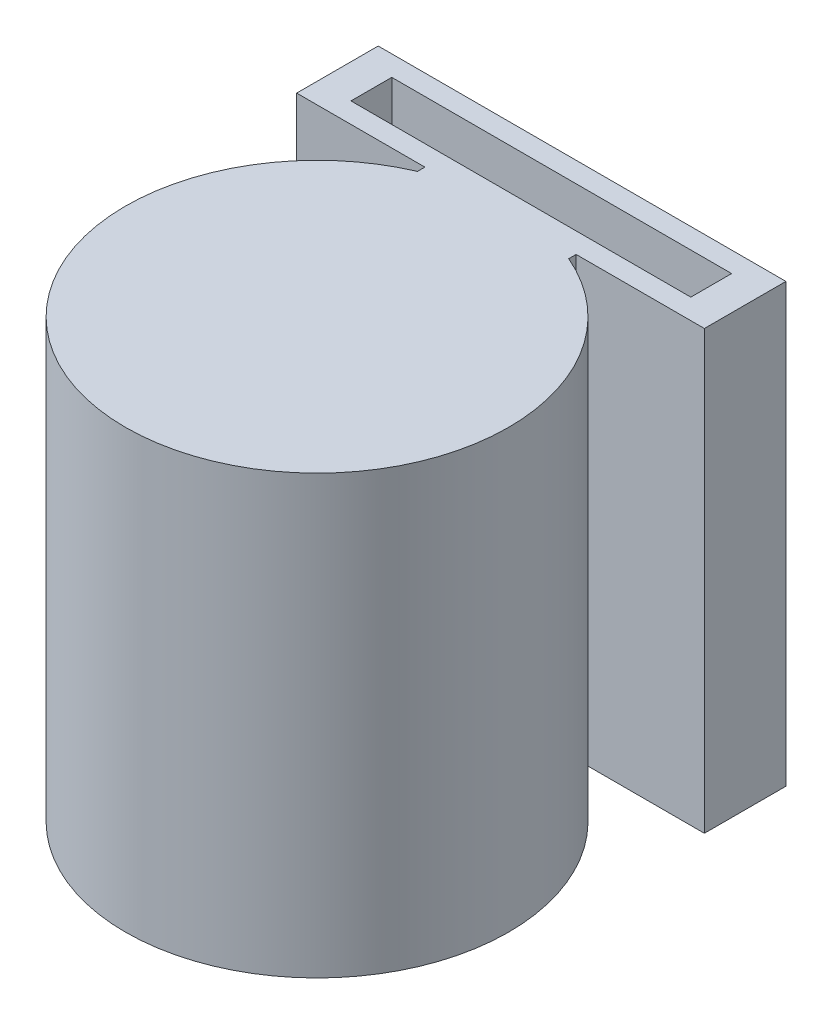
SolidWorks part; units mm, degrees
ref_plane "Alzado" through (0, 0, 0) normal (0, 0, 1) x (1, 0, 0)
ref_plane "Planta" through (0, 0, 0) normal (0, 1, 0) x (1, 0, 0)
ref_plane "Vista lateral" through (0, 0, 0) normal (1, 0, 0) x (0, 0, -1)
sketch "Croquis1" plane through (0, 0, 0) normal (0, 1, 0) x (1, 0, 0)
  line L0 (-15, 28) -> (-15, 22)
  line L1 (-15, 22) -> (15, 22)
  line L2 (15, 22) -> (15, 28)
  line L3 (15, 28) -> (-15, 28)
  line L4 (-12.503, 26.502) -> (-12.503, 23.498)
  line L5 (-12.503, 23.498) -> (12.503, 23.498)
  line L6 (12.503, 23.498) -> (12.503, 26.502)
  line L7 (12.503, 26.502) -> (-12.503, 26.502)
  line L8 (0, 22) -> (0, 0) construction
  dimension "D1" = 30
  dimension "D2" = 6
  dimension "D3" = 2.497
  dimension "D4" = 1.498
  dimension "D5" = 25.006
  dimension "D6" = 3.004
  dimension "D7" = 22
extrude "Saliente-Extruir1" add sketch "Croquis1" against normal blind 32.17 separate body
sketch "Croquis27" plane through (0, 0, -28) normal (0, 0, -1) x (-1, 0, 0)
  line L0 (0, -1.9214) -> (0, -33.4148) construction
  line L2 (14.9659, -17.6681) -> (-14.9659, -17.6681) construction
sketch "Croquis2" plane through (0, 0, -28) normal (0, 0, -1) x (1, 0, 0)
  line L0 (0, 17.6681) -> (4.7642, 17.6681) construction
  line L1 (-12.5, 5.1662) -> (12.5, 5.1662)
  line L2 (-12.5, 5.1662) -> (-12.5, 30.17)
  line L3 (-12.5, 30.17) -> (12.5, 30.17)
  line L4 (12.5, 5.1662) -> (12.5, 30.17)
  line L5 (15, 32.17) -> (15, 0) construction
  line L7 (-14.9659, 17.6681) -> (14.9659, 17.6681) construction
  line L9 (-12.5, 30.17) -> (12.5, 5.1662) construction
  line L10 (12.5, 30.17) -> (-12.5, 5.1662) construction
  line L11 (15, 32.17) -> (-15, 32.17) construction
  dimension "D1" = 2
  dimension "D3" = 2.5
  dimension "D4" = 25
extrude "Cortar-Extruir1" cut sketch "Croquis2" against normal up to surface (1.498 mm away) up to face at (0, -16.085, -26.502)
sketch "Croquis3" plane through (0, 0, 0) normal (0, 1, 0) x (1, 0, 0)
  line L0 (0, 8.4997) -> (0, 22) construction
  line L1 (-15, 22) -> (15, 22) construction
  circle A0 centre (0, 8.4997) radius 14.0984
  circle A1 centre (0, 8.4997) radius 13.1
  dimension "D1" = 26.2
  dimension "D2" = 0.9984
  dimension "D3" = 13.5003
extrude "Saliente-Extruir2" add sketch "Croquis3" against normal up to surface (32.17 mm away) up to face at (0, -32.17, -25)
ref_plane "Plano1" through (0, 0, 5.5987) normal (0, 0, 1) x (1, 0, 0)
sketch "Croquis24" plane through (0, 0, 0) normal (0, 1, 0) x (1, 0, 0)
  line L0 (0, 22) -> (0, 8.4997) construction
  line L1 (-4.0629, 22) -> (4.0629, 22) construction
sketch "Croquis17" plane through (0, 0, 0) normal (1, 0, 0) x (0, 0, -1)
  line L0 (-10.17, -32.17) -> (25.83, 3.83)
  line L2 (25.83, 3.83) -> (25.83, -32.17)
  line L3 (25.83, -32.17) -> (-10.17, -32.17)
  line L4 (22, -32.17) -> (28, -32.17) construction
  dimension "D1" = 36
  dimension "D3" = 45
ref_plane "Plano3" through (0, 0, -25.83) normal (0, 0, -1) x (-1, 0, 0)
sketch "Croquis19" plane through (0, 0, -25.83) normal (0, 0, -1) x (-1, 0, 0)
  line L0 (0, 3.83) -> (21.1813, 3.83)
ref_plane "Plano2" through (0, -11, -11) normal (0, -0.7071, -0.7071) x (-1, 0, 0)
sketch "Croquis10" plane through (0, -11, -11) normal (0, -0.7071, -0.7071) x (-1, 0, 0)
  line L1 (-15.7096, 15.2733) -> (14.4682, 15.2733)
  line L2 (-15.7096, 15.2733) -> (-15.7096, -26.0005)
  line L3 (-15.7096, -26.0005) -> (14.4682, -26.0005)
  line L4 (14.4682, 15.2733) -> (14.4682, -26.0005)
  ellipse E1 centre (0, -16.7374) end of major axis (-13.1, -16.7374) minor radius 9.2631 construction
  ellipse E2 centre (0, 6.0102) end of major axis (13.1, 6.0102) minor radius 9.2631 construction
extrude "Saliente-Extruir4" add sketch "Croquis10" against normal blind 22
sketch "Croquis11" plane through (0, -32.17, 0) normal (0, -1, 0) x (1, 0, 0)
  line L0 (-4.6767, -21.7998) -> (-14.4682, -21.7998)
  line L1 (15.7096, -21.7998) -> (4.6767, -21.7998)
  line L2 (15.7096, -21.7998) -> (15.7096, 22.9415)
  line L3 (15.7096, 22.9415) -> (-14.4682, 22.9415)
  line L4 (-14.4682, -21.7998) -> (-14.4682, 22.9415)
  arc A0 (4.6767, -21.7998) -> (-4.6767, -21.7998) centre (0, -8.4997) ccw
  arc A1 (4.0629, -22) -> (-4.0629, -22) centre (0, -8.4997) ccw construction
extrude "Cortar-Extruir2" cut sketch "Croquis11" against normal blind 58 and the other way blind 10
sketch "Croquis12" plane through (0, 0, 0) normal (1, 0, 0) x (0, 0, -1)
  line L1 (28, 0) -> (-15.0912, 0)
  line L2 (28, 0) -> (28, 18.5635)
  line L3 (28, 18.5635) -> (-15.0912, 18.5635)
  line L4 (-15.0912, 0) -> (-15.0912, 18.5635)
extrude "Cortar-Extruir3" cut sketch "Croquis12" against normal blind 58 and the other way blind 58
sketch "Croquis23" plane through (0, 0, 0) normal (0, 1, 0) x (1, 0, 0)
  line L0 (-15, 22) -> (-4.0629, 22) construction
  line L1 (-5.5629, 22) -> (-4.0629, 22)
  line L2 (4.0629, 22) -> (15, 22) construction
  line L3 (4.0629, 22) -> (5.5629, 22)
  line L4 (-5.5629, 22) -> (-5.5629, 21.4542)
  line L6 (5.5629, 21.4542) -> (5.5629, 22)
  arc A0 (-4.0629, 22) -> (4.0629, 22) centre (0, 8.4997) ccw construction
  arc A1 (-4.0629, 22) -> (-5.5629, 21.4542) centre (0, 8.4997) ccw
  arc A2 (5.5629, 21.4542) -> (4.0629, 22) centre (0, 8.4997) ccw
  dimension "D1" = 1.5
extrude "Saliente-Extruir6" add sketch "Croquis23" against normal through all
sketch "Croquis22" plane through (0, 0, -23.498) normal (0, 0, 1) x (1, 0, 0)
  circle A0 centre (0, -17.33) radius 5
  dimension "D1" = 10
extrude "Cortar-Extruir6" cut sketch "Croquis22" along normal blind 4
